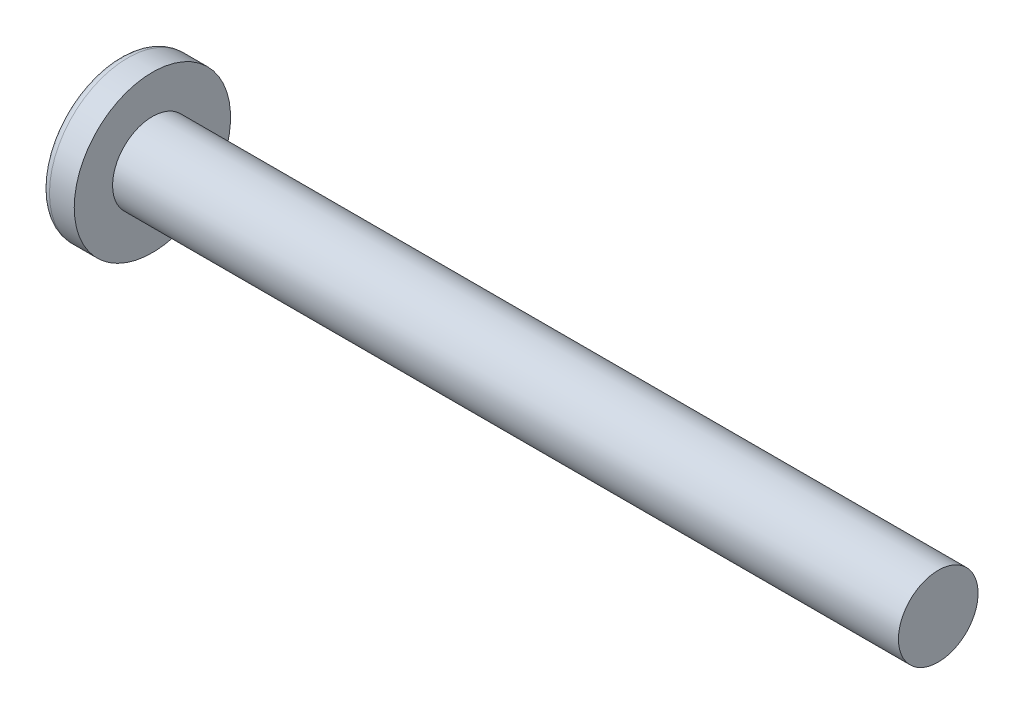
SolidWorks part; units mm, degrees
ref_plane "Plane1" through (0, 0, 0) normal (0, 0, 1) x (1, 0, 0)
ref_plane "Plane2" through (0, 0, 0) normal (0, 1, 0) x (1, 0, 0)
ref_plane "Plane3" through (0, 0, 0) normal (1, 0, 0) x (0, 0, -1)
sketch "BodySke" plane through (0, 0, 0) normal (0, 0, 1) x (1, 0, 0)
  line L0 (3.3782, 2.413) -> (3.3782, 4.7371)
  line L1 (3.9078, 6.35) -> (3.9078, -3.175) construction
  line L2 (-25.4, 0) -> (127, 0) construction
  line L3 (51.0032, 0) -> (0, 0)
  line L4 (3.3782, 2.413) -> (51.0032, 2.413)
  line L5 (51.0032, 2.413) -> (51.0032, 0)
  line L6 (1.8777, 4.7371) -> (3.3782, 4.7371)
  line L7 (3.3782, -2.413) -> (51.0032, -2.413) construction
  line L8 (25.6032, 6.35) -> (25.6032, -3.175) construction
  arc A0 (1.4662, 4.5269) -> (0, 0) centre (7.7216, 0) ccw
  arc A2 (1.4662, 4.5269) -> (1.8777, 4.7371) centre (1.8777, 4.2291) cw
  dimension "Head_fillet_rad" = 0.508
  dimension "Head_crown_rad" = 7.7216
  dimension "Head_ht" = 3.3782
  dimension "Diameter" = 4.826
  dimension "Length" = 47.625
  dimension "Head_dia" = 9.4742
  dimension "Advance" = 1.0592
  dimension "Thread_nom" = 25.4
revolve "Base-Revolve" add sketch "BodySke" angle 360 about L2
cosmetic thread "ThreadCosmetic" [suppressed] parameters "Thread_length"=25.4, "Thread_minor"=3.5662
sketch "Sketch3" plane through (0, 0, 0) normal (1, 0, 0) x (0, 0, -1)
  line L0 (0.5842, -3.048) -> (-0.5842, -3.048)
  line L1 (0.5842, -3.048) -> (0.5842, 3.048)
  line L2 (-0.5842, 3.048) -> (0.5842, 3.048)
  line L3 (-0.5842, 3.048) -> (-0.5842, -3.048)
  dimension "D1" = 3.048
  dimension "Cross_dia" = 6.096
  dimension "D2" = 0.5842
  dimension "Cross_width" = 1.1684
ref_plane "Plane4" through (3.4798, 0, 0) normal (1, 0, 0) x (0, 0, -1)
sketch "Sketch4" plane through (3.4798, 0, 0) normal (1, 0, 0) x (0, 0, -1)
  line L0 (0.2921, -0.2921) -> (-0.2921, -0.2921)
  line L1 (0.2921, -0.2921) -> (0.2921, 0.2921)
  line L2 (-0.2921, 0.2921) -> (0.2921, 0.2921)
  line L3 (-0.2921, 0.2921) -> (-0.2921, -0.2921)
  dimension "D1" = 0.5842
  dimension "D2" = 0.5842
  dimension "D3" = 0.2921
  dimension "D4" = 0.2921
loft "Cut-Loft1" cut profiles "Sketch3", "Sketch4"
pattern_circular "CirPattern1" count 2 every 90 about axis through (0, 0, 0) along (1, 0, 0) of "Cut-Loft1"
sketch "ThdSchSke" plane through (0, 0, 0) normal (0, 0, 1) x (1, 0, 0)
  line L0 (25.6032, -1.7831) -> (25.1621, -2.413)
  line L1 (25.6032, -1.7831) -> (26.0443, -2.413)
  line L2 (26.0443, -2.413) -> (26.0443, -3.0162)
  line L3 (-3.175, 0) -> (5.1513, 0) construction
  line L5 (26.0443, -3.0162) -> (25.1621, -3.0162)
  line L6 (25.1621, -3.0162) -> (25.1621, -2.413)
  dimension "Thread_minor" = 3.5662
  dimension "Diameter" = 4.826
  dimension "Start" = 25.6032
  dimension "SideAngle" = 55
  dimension "VeeAngle" = 70
  dimension "Overcut" = 6.0325
revolve "ThreadSchematic" [suppressed] cut sketch "ThdSchSke" angle 360 about L3
pattern_linear "ThdSchPat" [suppressed]
equation "\"D1@Sketch3\" = \"Cross_dia@Sketch3\" / 2"
equation "\"D2@Sketch3\" = \"Cross_width@Sketch3\" / 2"
equation "\"D1@Sketch4\" = \"Cross_width@Sketch3\" *.5"
equation "\"D2@Sketch4\" = \"D1@Sketch4\""
equation "\"D3@Sketch4\" = \"D1@Sketch4\" / 2"
equation "\"D4@Sketch4\" = \"D2@Sketch4\" / 2"
equation "\"Thread_length@ThreadCosmetic\" = ((sgn( (\"Length@BodySke\" - \"Advance@BodySke\" ) - \"Thread_nom@BodySke\" )-1)*( (\"Length@BodySke\" - \"Advance@BodySke\" ) - \"Thread_nom@BodySke\" ))/-2+ \"Thread_nom@BodySke\""
equation "\"Thread_minor@ThdSchSke\" = \"Thread_minor@ThreadCosmetic\""
equation "\"Diameter@ThdSchSke\" = \"Diameter@BodySke\""
equation "\"Overcut@ThdSchSke\" = \"Diameter@BodySke\" * 1.25"
equation "\"Start@ThdSchSke\" = \"Head_ht@BodySke\" + \"Length@BodySke\" - \"Thread_length@ThreadCosmetic\"  '---Non-countersunk---"
equation "\"Num_threads@ThdSchPat\" = int( \"Thread_length@ThreadCosmetic\" / \"Advance@BodySke\" + 0.999 )  + 1"
equation "\"Advance@ThdSchPat\" = \"Thread_length@ThreadCosmetic\" /  (\"Num_threads@ThdSchPat\" - 1) 'relax it"
